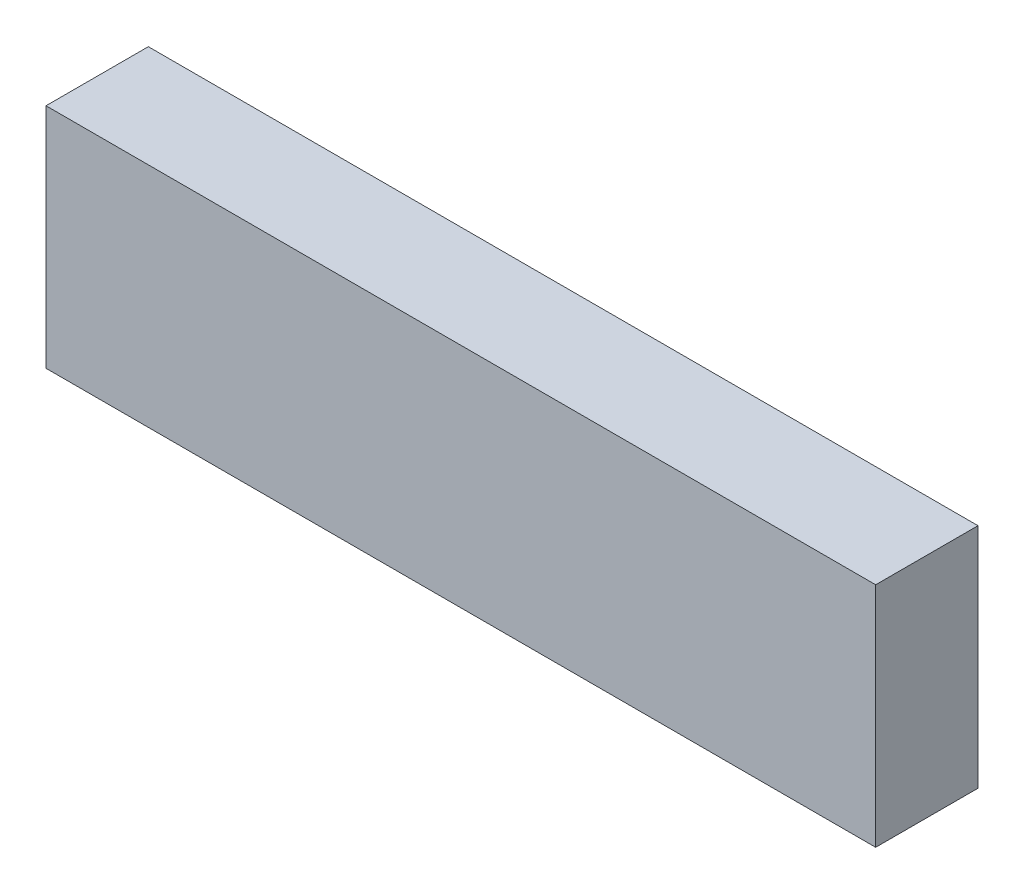
SolidWorks part; units mm, degrees
ref_plane "Front" through (0, 0, 0) normal (0, 0, 1) x (1, 0, 0)
ref_plane "Top" through (0, 0, 0) normal (0, 1, 0) x (1, 0, 0)
ref_plane "Right" through (0, 0, 0) normal (1, 0, 0) x (0, 0, -1)
sketch "Sketch1" plane through (0, 0, 0) normal (0, 0, 1) x (1, 0, 0)
  line L1 (0, 0) -> (1.5, 0)
  line L2 (0, 0) -> (0, 0.4111)
  line L3 (0, 0.4111) -> (1.5, 0.4111)
  line L4 (1.5, 0) -> (1.5, 0.4111)
  dimension "D1" = 1.5
  dimension "D2" = 0.4111
extrude "Boss-Extrude1" add sketch "Sketch1" along normal blind 0.185
sketch "Sketch2" plane through (0, 0.4111, 0) normal (0, 1, 0) x (1, 0, 0)
  line L4 (1.5, 0) -> (0, 0)
  line L5 (0, 0) -> (0, -0.185)
  line L6 (0, -0.185) -> (1.5, -0.185)
  line L7 (1.5, -0.185) -> (1.5, 0)
  line L8 (1.5, 0) -> (0, 0)
  line L9 (0, 0) -> (0, -0.185)
  line L10 (0, -0.185) -> (1.5, -0.185)
  line L11 (1.5, -0.185) -> (1.5, 0)
  dimension "D1" = 0
